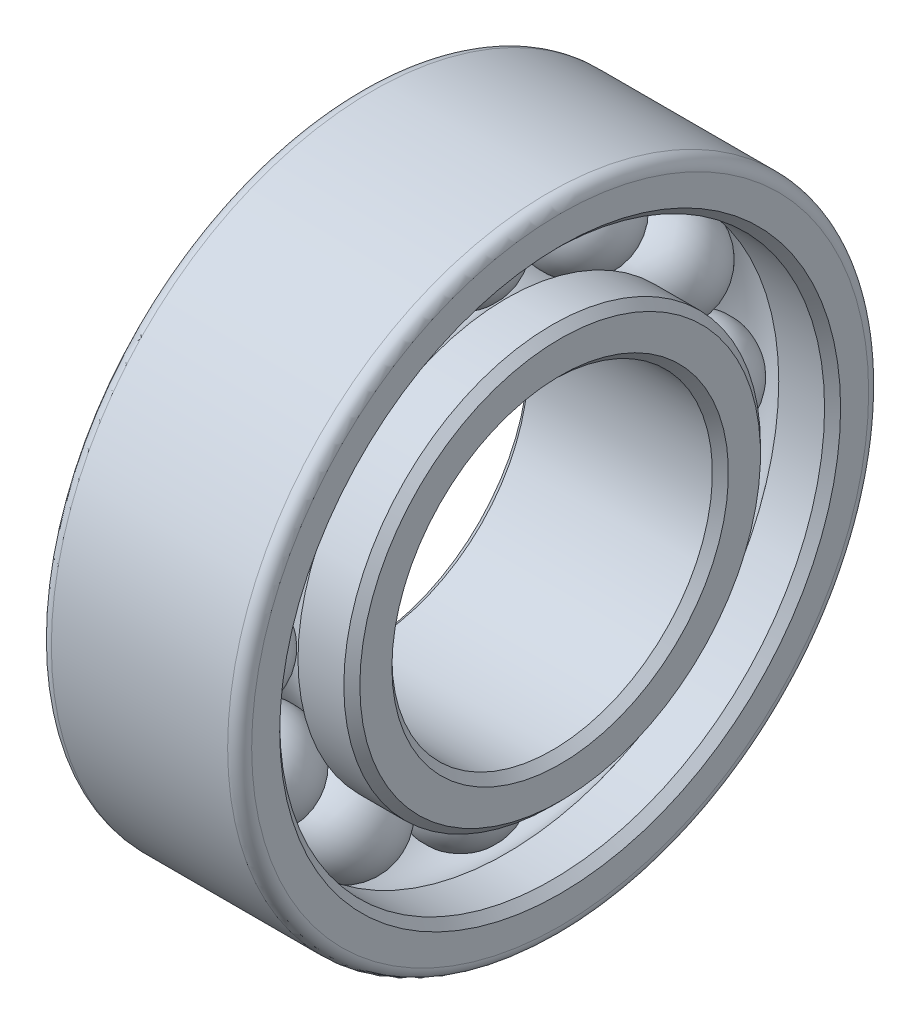
SolidWorks part; units mm, degrees
material "1023 Листовая углеродистая сталь (SS)"
ref_plane "Спереди" through (0, 0, 0) normal (0, 0, 1) x (1, 0, 0)
ref_plane "Сверху" through (0, 0, 0) normal (0, 1, 0) x (1, 0, 0)
ref_plane "Справа" through (0, 0, 0) normal (1, 0, 0) x (0, 0, -1)
sketch "Эскиз1" plane through (0, 0, 0) normal (0, 0, 1) x (1, 0, 0)
  line L0 (-1.0669, -4) -> (5.2077, -4) construction
  line L1 (0, 0) -> (5, 0)
  line L2 (0, 0) -> (0, 1.2)
  line L3 (0, 1.2) -> (1.3649, 1.2)
  line L4 (5, 0) -> (5, 1.2)
  line L5 (0, 2.8) -> (1.3649, 2.8)
  line L6 (0, 2.8) -> (0, 4)
  line L7 (0, 4) -> (5, 4)
  line L8 (5, 2.8) -> (5, 4)
  line L9 (3.6564, 2.8) -> (5, 2.8)
  line L10 (3.6564, 1.2) -> (5, 1.2)
  arc A0 (1.3649, 1.2) -> (3.6564, 1.2) centre (2.5106, 2) ccw
  arc A1 (3.6564, 2.8) -> (1.3649, 2.8) centre (2.5106, 2) ccw
  dimension "D7" = 2
  dimension "D8" = 0
  dimension "D9" = 1.3974
  dimension "D1" = 4
  dimension "D2" = 5
  dimension "D3" = 1.2
  dimension "D4" = 5
  dimension "D5" = 1.2
  dimension "D6" = 8
  dimension "D10" = 2.4894
revolve "Повернуть1" add sketch "Эскиз1" angle 360 about L0
sketch "Эскиз2" plane through (0, 0, 0) normal (0, 0, 1) x (1, 0, 0)
  line L0 (2.5106, 3.1026) -> (2.5106, 0.6026) construction
  line L1 (2.5106, 3.1026) -> (2.5106, 0.6026)
  arc A0 (2.5106, 3.1026) -> (2.5106, 0.6026) centre (2.5106, 1.8526) ccw
  arc A1 (1.3649, 1.2) -> (3.6564, 1.2) centre (2.5106, 2) ccw construction
  dimension "D1" = 1.25
revolve "Повернуть2" add sketch "Эскиз2" angle 360 about L0
pattern_circular "Круговой массив5" count 12 over 360 about axis through (0, -4, 0) along (1, 0, 0) of bodies 105
fillet "Скругление1" radius 0.3 2 edges at (5, -4, 8) (0, -4, 8)
chamfer "Фаска1" distance 0.2 angle 45 4 edges at (0, -4, 4) (5, -4, 4) (5, -4, 5.2) (0, -4, 5.2)
chamfer "Фаска2" distance 0.2 angle 45 2 edges at (5, -4, 6.8) (0, -4, 6.8)
